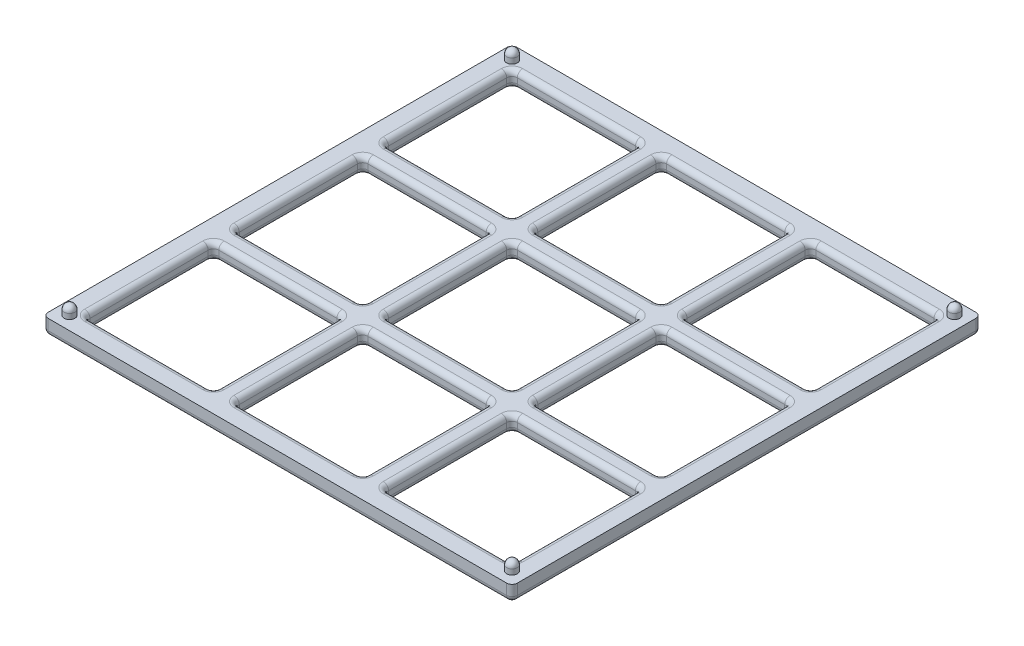
SolidWorks part; units mm, degrees
ref_plane "Front Plane" through (0, 0, 0) normal (0, 0, 1) x (1, 0, 0)
ref_plane "Top Plane" through (0, 0, 0) normal (0, 1, 0) x (1, 0, 0)
ref_plane "Right Plane" through (0, 0, 0) normal (1, 0, 0) x (0, 0, -1)
sketch "Sketch1" plane through (0, 0, 0) normal (0, 1, 0) x (1, 0, 0)
  line L1 (-69.85, -69.85) -> (69.85, -69.85)
  line L2 (-69.85, -69.85) -> (-69.85, 69.85)
  line L3 (-69.85, 69.85) -> (69.85, 69.85)
  line L4 (69.85, -69.85) -> (69.85, 69.85)
  line L5 (-69.85, -69.85) -> (69.85, 69.85) construction
  line L6 (-69.85, 69.85) -> (69.85, -69.85) construction
  point P0 (0, 0)
  dimension "D1" = 139.7
  dimension "D2" = 139.7
extrude "Boss-Extrude1" add sketch "Sketch1" along normal blind 4.7625
sketch "Sketch2" plane through (0, 4.7625, 0) normal (0, 1, 0) x (1, 0, 0)
  line L0 (69.85, 69.85) -> (-69.85, 69.85) construction
  line L1 (-63.627, 63.627) -> (-25.273, 63.627)
  line L2 (-63.627, 63.627) -> (-63.627, 25.273)
  line L3 (-63.627, 25.273) -> (-25.273, 25.273)
  line L4 (-25.273, 63.627) -> (-25.273, 25.273)
  line L5 (-63.627, 63.627) -> (-25.273, 25.273) construction
  line L6 (-63.627, 25.273) -> (-25.273, 63.627) construction
  line L7 (-69.85, 69.85) -> (-69.85, -69.85) construction
  line L8 (-19.177, 63.627) -> (19.177, 63.627)
  line L9 (-19.177, 63.627) -> (-19.177, 25.273)
  line L10 (-19.177, 25.273) -> (19.177, 25.273)
  line L11 (19.177, 63.627) -> (19.177, 25.273)
  line L12 (-19.177, 63.627) -> (19.177, 25.273) construction
  line L13 (-19.177, 25.273) -> (19.177, 63.627) construction
  line L14 (25.273, 63.627) -> (63.627, 63.627)
  line L15 (25.273, 63.627) -> (25.273, 25.273)
  line L16 (25.273, 25.273) -> (63.627, 25.273)
  line L17 (63.627, 63.627) -> (63.627, 25.273)
  line L18 (25.273, 63.627) -> (63.627, 25.273) construction
  line L19 (25.273, 25.273) -> (63.627, 63.627) construction
  line L20 (-19.177, 19.177) -> (19.177, 19.177)
  line L21 (-19.177, 19.177) -> (-19.177, -19.177)
  line L22 (-19.177, -19.177) -> (19.177, -19.177)
  line L23 (19.177, 19.177) -> (19.177, -19.177)
  line L24 (-19.177, 19.177) -> (19.177, -19.177) construction
  line L25 (-19.177, -19.177) -> (19.177, 19.177) construction
  line L26 (25.273, 19.177) -> (63.627, 19.177)
  line L27 (25.273, 19.177) -> (25.273, -19.177)
  line L28 (25.273, -19.177) -> (63.627, -19.177)
  line L29 (63.627, 19.177) -> (63.627, -19.177)
  line L30 (25.273, 19.177) -> (63.627, -19.177) construction
  line L31 (25.273, -19.177) -> (63.627, 19.177) construction
  line L32 (-19.177, -25.273) -> (19.177, -25.273)
  line L33 (-19.177, -25.273) -> (-19.177, -63.627)
  line L34 (-19.177, -63.627) -> (19.177, -63.627)
  line L35 (19.177, -25.273) -> (19.177, -63.627)
  line L36 (-19.177, -25.273) -> (19.177, -63.627) construction
  line L37 (-19.177, -63.627) -> (19.177, -25.273) construction
  line L38 (25.273, -25.273) -> (63.627, -25.273)
  line L39 (25.273, -25.273) -> (25.273, -63.627)
  line L40 (25.273, -63.627) -> (63.627, -63.627)
  line L41 (63.627, -25.273) -> (63.627, -63.627)
  line L42 (25.273, -25.273) -> (63.627, -63.627) construction
  line L43 (25.273, -63.627) -> (63.627, -25.273) construction
  line L44 (-63.627, 19.177) -> (-25.273, 19.177)
  line L45 (-63.627, 19.177) -> (-63.627, -19.177)
  line L46 (-63.627, -19.177) -> (-25.273, -19.177)
  line L47 (-25.273, 19.177) -> (-25.273, -19.177)
  line L48 (-63.627, 19.177) -> (-25.273, -19.177) construction
  line L49 (-63.627, -19.177) -> (-25.273, 19.177) construction
  line L50 (-63.627, -25.273) -> (-25.273, -25.273)
  line L51 (-63.627, -25.273) -> (-63.627, -63.627)
  line L52 (-63.627, -63.627) -> (-25.273, -63.627)
  line L53 (-25.273, -25.273) -> (-25.273, -63.627)
  line L54 (-63.627, -25.273) -> (-25.273, -63.627) construction
  line L55 (-63.627, -63.627) -> (-25.273, -25.273) construction
  point P0 (-44.45, 44.45)
  point P11 (0, 44.45)
  point P16 (44.45, 44.45)
  point P21 (0, 0)
  point P26 (44.45, 0)
  point P31 (0, -44.45)
  point P36 (44.45, -44.45)
  point P41 (-44.45, 0)
  point P46 (-44.45, -44.45)
  dimension "D1" = 38.354
  dimension "D2" = 38.354
  dimension "D3" = 6.223
  dimension "D4" = 6.223
  dimension "D5" = 3
  dimension "D6" = 3
extrude "Cut-Extrude1" cut sketch "Sketch2" against normal blind 4.7625
fillet "Fillet2" radius 1.5875 116 edges at (69.85, 2.3813, -69.85) (-69.85, 2.3813, -69.85) (-69.85, 2.3813, 69.85) (69.85, 2.3813, 69.85) (0, 0, 69.85) (-69.85, 0, 0) (0, 0, -69.85) (69.85, 0, 0) (-25.273, 2.3813, -25.273) (-63.627, 2.3813, -25.273) (-63.627, 2.3813, -63.627) (-25.273, 2.3813, -63.627) (-44.45, 0, -25.273) (-63.627, 0, -44.45) (-44.45, 0, -63.627) (-25.273, 0, -44.45) (-44.45, 4.7625, -25.273) (-63.627, 4.7625, -44.45) (-44.45, 4.7625, -63.627) (-25.273, 4.7625, -44.45) (19.177, 2.3813, -25.273) (-19.177, 2.3813, -25.273) (-19.177, 2.3813, -63.627) (19.177, 2.3813, -63.627) (0, 0, -25.273) (-19.177, 0, -44.45) (0, 0, -63.627) (19.177, 0, -44.45) (0, 4.7625, -25.273) (-19.177, 4.7625, -44.45) (0, 4.7625, -63.627) (19.177, 4.7625, -44.45) (63.627, 2.3813, -25.273) (25.273, 2.3813, -25.273) (25.273, 2.3813, -63.627) (63.627, 2.3813, -63.627) (44.45, 0, -25.273) (25.273, 0, -44.45) (44.45, 0, -63.627) (63.627, 0, -44.45) (44.45, 4.7625, -25.273) (25.273, 4.7625, -44.45) (44.45, 4.7625, -63.627) (63.627, 4.7625, -44.45) (19.177, 2.3813, 19.177) (-19.177, 2.3813, 19.177) (-19.177, 2.3813, -19.177) (19.177, 2.3813, -19.177) (0, 0, 19.177) (-19.177, 0, 0) (0, 0, -19.177) (19.177, 0, 0) (0, 4.7625, 19.177) (-19.177, 4.7625, 0) (0, 4.7625, -19.177) (19.177, 4.7625, 0) (63.627, 2.3813, 19.177) (25.273, 2.3813, 19.177) (25.273, 2.3813, -19.177) (63.627, 2.3813, -19.177) (44.45, 0, 19.177) (25.273, 0, 0) (44.45, 0, -19.177) (63.627, 0, 0) (44.45, 4.7625, 19.177) (25.273, 4.7625, 0) (44.45, 4.7625, -19.177) (63.627, 4.7625, 0) (19.177, 2.3813, 63.627) (-19.177, 2.3813, 63.627) (-19.177, 2.3813, 25.273) (19.177, 2.3813, 25.273) (0, 0, 63.627) (-19.177, 0, 44.45) (0, 0, 25.273) (19.177, 0, 44.45) (0, 4.7625, 63.627) (-19.177, 4.7625, 44.45) (0, 4.7625, 25.273) (19.177, 4.7625, 44.45) (63.627, 2.3813, 63.627) (25.273, 2.3813, 63.627) (25.273, 2.3813, 25.273) (63.627, 2.3813, 25.273) (44.45, 0, 63.627) (25.273, 0, 44.45) (44.45, 0, 25.273) (63.627, 0, 44.45) (44.45, 4.7625, 63.627) (25.273, 4.7625, 44.45) (44.45, 4.7625, 25.273) (63.627, 4.7625, 44.45) (-25.273, 2.3813, 19.177) (-63.627, 2.3813, 19.177) (-63.627, 2.3813, -19.177) (-25.273, 2.3813, -19.177) (-44.45, 0, 19.177) (-63.627, 0, 0) (-44.45, 0, -19.177) (-25.273, 0, 0) (-44.45, 4.7625, 19.177) (-63.627, 4.7625, 0) (-44.45, 4.7625, -19.177) (-25.273, 4.7625, 0) (-25.273, 2.3813, 63.627) (-63.627, 2.3813, 63.627) (-63.627, 2.3813, 25.273) (-25.273, 2.3813, 25.273) (-44.45, 0, 63.627) (-63.627, 0, 44.45) (-44.45, 0, 25.273) (-25.273, 0, 44.45) (-44.45, 4.7625, 63.627) (-63.627, 4.7625, 44.45) (-44.45, 4.7625, 25.273) (-25.273, 4.7625, 44.45)
sketch "Sketch3" plane through (0, 4.7625, 0) normal (0, 1, 0) x (1, 0, 0)
  line L0 (-68.2625, -69.85) -> (68.2625, -69.85) construction
  line L1 (-69.85, 68.2625) -> (-69.85, -68.2625) construction
  line L2 (69.85, -68.2625) -> (69.85, 68.2625) construction
  line L3 (68.2625, 69.85) -> (-68.2625, 69.85) construction
  circle A0 centre (-65.8813, 65.8813) radius 1.5875
  circle A1 centre (65.8813, 65.8813) radius 1.5875
  circle A2 centre (65.8813, -65.8813) radius 1.5875
  circle A3 centre (-65.8813, -65.8813) radius 1.5875
  dimension "D3" = 3.175
  dimension "D4" = 3.9688
  dimension "D5" = 3.9688
  dimension "D6" = 3.175
  dimension "D7" = 3.9688
  dimension "D8" = 3.9688
  dimension "D9" = 3.175
  dimension "D10" = 3.9688
  dimension "D11" = 3.9688
  dimension "D12" = 3.175
  dimension "D1" = 3.9688
  dimension "D2" = 3.9688
extrude "Boss-Extrude2" add sketch "Sketch3" along normal blind 3.175
fillet "Fillet3" radius 1.5875 4 edges at (65.8813, 7.9375, 67.4688) (65.8813, 7.9375, -64.2938) (-65.8813, 7.9375, 67.4688) (-65.8813, 7.9375, -64.2938)
